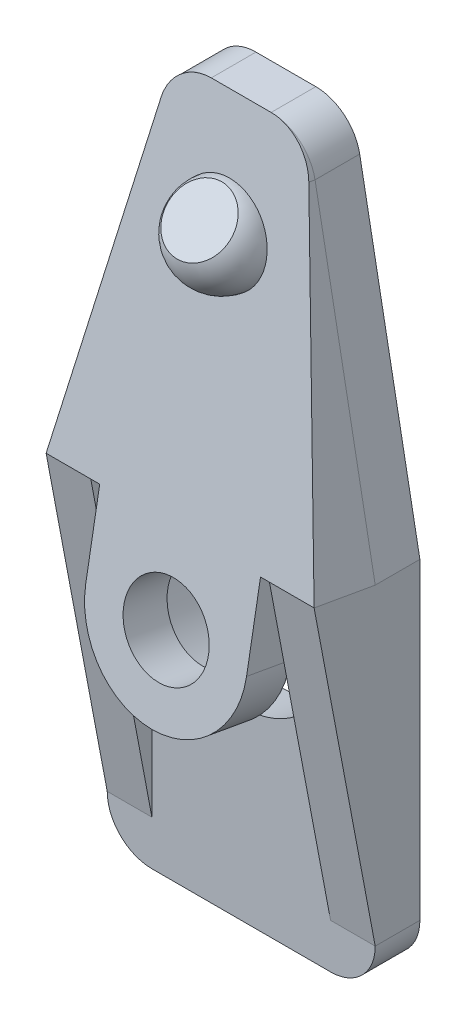
SolidWorks part; units mm, degrees
ref_plane "Front Plane" through (0, 0, 0) normal (0, 0, 1) x (1, 0, 0)
ref_plane "Top Plane" through (0, 0, 0) normal (0, 1, 0) x (1, 0, 0)
ref_plane "Right Plane" through (0, 0, 0) normal (1, 0, 0) x (0, 0, -1)
sketch "Sketch1" plane through (0, 0, 0) normal (0, 0, 1) x (1, 0, 0)
  line L0 (0, 0) -> (0, -10486.1436) construction
  line L1 (-4, -10) -> (4, -10)
  line L2 (6, -8) -> (6, 6)
  line L3 (6, 6) -> (3.3059, 20.3686)
  line L4 (1.3401, 22) -> (-1.3401, 22)
  line L5 (-6, 6) -> (-3.3059, 20.3686)
  line L6 (-6, -8) -> (-6, 6)
  arc A0 (3.3059, 20.3686) -> (1.3401, 22) centre (1.3401, 20) ccw
  arc A1 (4, -10) -> (6, -8) centre (4, -8) ccw
  arc A2 (-4, -10) -> (-6, -8) centre (-4, -8) cw
  arc A3 (-3.3059, 20.3686) -> (-1.3401, 22) centre (-1.3401, 20) cw
  point P3 (-6, -10)
  point P10 (3, 22)
  point P13 (6, -10)
  point P14 (0, 0)
  point P21 (0, 22)
  point P22 (0, -10)
  point P23 (-3, 22)
  dimension "D5" = 2
  dimension "D1" = 3
  dimension "D2" = 6
  dimension "D3" = 32
  dimension "D4" = 16
  dimension "10" = 10
extrude "Boss-Extrude1" add sketch "Sketch1" along normal blind 2
ref_plane "Plane1" through (0, 1.0054, 5.7019) normal (0, 0.1736, 0.9848) x (-1, 0, 0)
sketch "Sketch2" plane through (0, 1.0054, 5.7019) normal (0, 0.1736, 0.9848) x (-1, 0, 0)
  line L0 (6, -5.5616) -> (-6, -5.5616) construction
  line L2 (-3.6, -1.9616) -> (-3.6, -5.5616)
  line L3 (-3.6, -5.5616) -> (-6, -5.5616)
  line L4 (3.6, -1.9616) -> (3.6, -5.5616)
  line L5 (3.6, -5.5616) -> (6, -5.5616)
  line L6 (-1.3401, -21.3185) -> (1.3401, -21.3185)
  line L7 (3.3059, -19.7118) -> (6, -5.5616)
  line L8 (6, -5.5616) -> (6, 8.2258)
  line L9 (4, 10.1954) -> (-4, 10.1954)
  line L10 (-6, 8.2258) -> (-6, -5.5616)
  line L11 (-6, -5.5616) -> (-3.3059, -19.7118)
  line L12 (-1.3401, -21.3185) -> (1.3401, -21.3185)
  line L13 (3.3059, -19.7118) -> (6, -5.5616)
  line L17 (-6, -5.5616) -> (-3.3059, -19.7118)
  arc A0 (3.6, -1.9616) -> (-3.6, -1.9616) centre (0, -1.9616) ccw
  circle A3 centre (0, -1.9616) radius 1.9
  ellipse E4 centre (-1.3401, -19.3489) end of major axis (0.6599, -19.3489) minor radius 1.9696 (-3.3059, -19.7118) -> (-1.3401, -21.3185) ccw
  ellipse E5 centre (1.3401, -19.3489) end of major axis (3.3401, -19.3489) minor radius 1.9696 (1.3401, -21.3185) -> (3.3059, -19.7118) ccw
  ellipse E6 centre (4, 8.2258) end of major axis (6, 8.2258) minor radius 1.9696 (6, 8.2258) -> (4, 10.1954) ccw
  ellipse E7 centre (-4, 8.2258) end of major axis (-2, 8.2258) minor radius 1.9696 (-4, 10.1954) -> (-6, 8.2258) ccw
  ellipse E8 centre (-1.3401, -19.3489) end of major axis (0.6599, -19.3489) minor radius 1.9696 (-3.3059, -19.7118) -> (-1.3401, -21.3185) ccw
  ellipse E9 centre (1.3401, -19.3489) end of major axis (3.3401, -19.3489) minor radius 1.9696 (1.3401, -21.3185) -> (3.3059, -19.7118) ccw
  point P26 (0, -5.5616)
  dimension "D2" = 7.2
  dimension "D5" = 3.8
  dimension "D3" = 2.4
  dimension "width" = 12
  dimension "D1" = 0
extrude "Boss-Extrude2" add sketch "Sketch2" against normal blind 2
sketch "Sketch4" plane through (0, 0.6581, 3.7323) normal (0, -0.1736, -0.9848) x (-1, 0, 0)
  circle A0 centre (0, 1.9616) radius 4
  dimension "D1" = 8
extrude "Cut-Extrude1" cut sketch "Sketch4" along normal up to next
sketch "Sketch5" plane through (0, 0.6581, 3.7323) normal (0, -0.1736, -0.9848) x (-1, 0, 0)
  line L7 (-6, 5.5616) -> (-3.6, 5.5616)
  line L8 (-3.6, 5.5616) -> (-3.6, 1.9616)
  line L9 (3.6, 1.9616) -> (3.6, 5.5616)
  line L10 (3.6, 5.5616) -> (6, 5.5616)
  line L11 (6, 5.5616) -> (5.1595, 9.9759)
  line L12 (5.1595, 9.9759) -> (-5.1595, 9.9759)
  line L13 (-5.1595, 9.9759) -> (-6, 5.5616)
  line L14 (-6, 5.5616) -> (-4, 5.5616)
  line L17 (4, 5.5616) -> (6, 5.5616)
  line L18 (6, 5.5616) -> (5.1595, 9.9759)
  line L19 (5.1595, 9.9759) -> (-5.1595, 9.9759)
  line L20 (-5.1595, 9.9759) -> (-6, 5.5616)
  arc A0 (-4, 5.5616) -> (4, 5.5616) centre (0, 1.9616) cw
  arc A1 (-3.6, 1.9616) -> (3.6, 1.9616) centre (0, 1.9616) ccw
  point P4 (0, 0)
  point P8 (3.6, 5.5616)
  point P9 (0, 0)
  point P13 (0, 0)
  dimension "D2" = 8
  dimension "D1" = 0
extrude "Boss-Extrude3" add sketch "Sketch5" along normal up to next
sketch "Sketch6" plane through (6, 0, 0) normal (1, 0, 0) x (0, 0, -1)
  line L0 (-4.7362, 6.4825) -> (-2, 6)
  line L1 (-4.7362, 6.4825) -> (-2.279, 20.4178) construction
  line L2 (-2.7665, 6.1352) -> (-4.7362, 6.4825) construction
  line L3 (-2, 6) -> (-2, -8)
  line L4 (-2, -8) -> (-4.7362, 6.4825)
extrude "Boss-Extrude4" add sketch "Sketch6" against normal blind 2
sketch "Sketch7" plane through (-6, 0, 0) normal (-1, 0, 0) x (0, 0, 1)
  line L0 (2, 6) -> (4.7362, 6.4825)
  line L1 (2.279, 20.4178) -> (4.7362, 6.4825) construction
  line L2 (2.7665, 6.1352) -> (4.7362, 6.4825) construction
  line L3 (4.7362, 6.4825) -> (2, -8)
  line L4 (2, -8) -> (2, 6)
extrude "Boss-Extrude5" add sketch "Sketch7" against normal blind 2
sketch "Sketch8" plane through (0, 0, 0) normal (0, 0, -1) x (-1, 0, 0)
  line L0 (-4, -3.5) -> (4, -3.5)
  line L2 (4, -5) -> (-4, -5)
  line L3 (-6, -8) -> (-6, 6) construction
  line L4 (6, 6) -> (6, -8) construction
  line L5 (4, -10) -> (-4, -10) construction
  line L6 (-4, -6.5) -> (4, -6.5)
  line L8 (4, -8) -> (-4, -8)
  arc A0 (-4, -3.5) -> (-4, -5) centre (-4, -4.25) ccw
  arc A1 (4, -5) -> (4, -3.5) centre (4, -4.25) ccw
  arc A2 (-4, -6.5) -> (-4, -8) centre (-4, -7.25) ccw
  arc A3 (4, -8) -> (4, -6.5) centre (4, -7.25) ccw
  point P13 (0, 0)
  point P14 (0, 0)
  point P15 (0, 0)
  point P16 (0, 0)
  point P22 (0, 0)
  point P23 (0, 0)
  point P24 (0, 0)
  dimension "D3" = 1.5
  dimension "D5" = 0.75
  dimension "D1" = 2
  dimension "D2" = 2
  dimension "D4" = 5
  dimension "D6" = 2
extrude "Cut-Extrude2" cut sketch "Sketch8" against normal blind 0.3
sketch "Sketch9" plane through (0, 1.0054, 5.7019) normal (0, 0.1736, 0.9848) x (1, 0, 0)
  line L0 (1.3401, 21.3185) -> (-1.3401, 21.3185) construction
  line L1 (0, 16.3185) -> (50000, 16.3185) construction
  line L2 (-2, 16.3185) -> (2, 16.3185)
  circle A0 centre (0, 16.3185) radius 2 construction
  arc A1 (-2, 16.3185) -> (2, 16.3185) centre (0, 16.3185) ccw
  dimension "D1" = 4
  dimension "D2" = 5
revolve "Revolve1" add sketch "Sketch9" angle 180 about L1
sketch "Sketch11" plane through (0, 0, 0) normal (1, 0, 0) x (0, 0, -1)
  line L0 (-4.8682, 17.076) -> (-2.8682, 19.076)
  line L1 (-2.8682, 19.076) -> (-5.7551, 19.076)
  line L2 (-5.7551, 19.076) -> (-4.8682, 17.076)
  arc A0 (-2.5209, 19.0456) -> (-3.2155, 15.1063) centre (-2.8682, 17.076) ccw construction
  point P5 (-5.7551, 19.076)
extrude "Cut-Extrude3" cut sketch "Sketch11" against normal through all both and the other way through all
